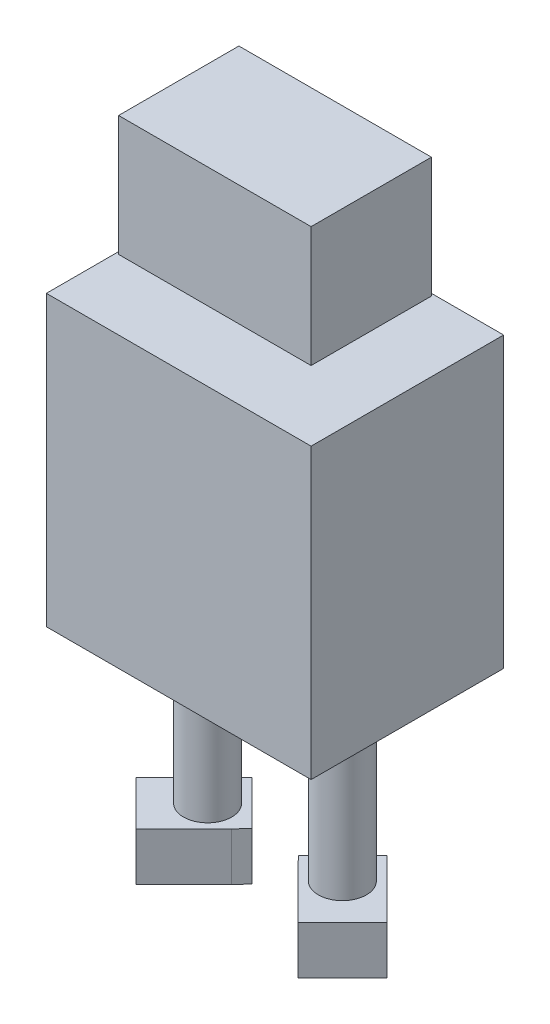
SolidWorks part; units mm, degrees
ref_plane "Front Plane" through (0, 0, 0) normal (0, 0, 1) x (1, 0, 0)
ref_plane "Top Plane" through (0, 0, 0) normal (0, 1, 0) x (1, 0, 0)
ref_plane "Right Plane" through (0, 0, 0) normal (1, 0, 0) x (0, 0, -1)
sketch "Sketch1" plane through (0, 0, 0) normal (0, 0, 1) x (1, 0, 0)
  line L1 (-27.5, -30) -> (27.5, -30)
  line L2 (-27.5, -30) -> (-27.5, 30)
  line L3 (-27.5, 30) -> (27.5, 30)
  line L4 (27.5, -30) -> (27.5, 30)
  line L5 (-27.5, -30) -> (27.5, 30) construction
  line L6 (-27.5, 30) -> (27.5, -30) construction
  point P0 (0, 0)
  dimension "D1" = 60
  dimension "D2" = 55
extrude "Boss-Extrude1" add sketch "Sketch1" along normal blind 40
sketch "Sketch2" plane through (0, 30, 0) normal (0, 1, 0) x (-1, 0, 0)
  line L0 (0, 40) -> (0, 0) construction
  line L1 (-27.5, 40) -> (27.5, 40) construction
  line L2 (-27.5, 0) -> (27.5, 0) construction
  line L3 (-27.5, 20) -> (27.5, 20) construction
  line L4 (-27.5, 40) -> (-27.5, 0) construction
  line L5 (27.5, 40) -> (27.5, 0) construction
  circle A0 centre (0, 20) radius 4
  dimension "D1" = 8
extrude "Boss-Extrude2" add sketch "Sketch2" along normal blind 7
sketch "Sketch4" plane through (0, 37, 0) normal (0, 1, 0) x (1, 0, 0)
  line L1 (20, -7.5) -> (-20, -7.5)
  line L2 (20, -7.5) -> (20, -32.5)
  line L3 (20, -32.5) -> (-20, -32.5)
  line L4 (-20, -7.5) -> (-20, -32.5)
  line L5 (20, -7.5) -> (-20, -32.5) construction
  line L6 (20, -32.5) -> (-20, -7.5) construction
  point P0 (0, -20)
  dimension "D1" = 25
  dimension "D2" = 40
extrude "Boss-Extrude3" add sketch "Sketch4" along normal blind 25
sketch "Sketch5" plane through (0, -30, 0) normal (0, -1, 0) x (1, 0, 0)
  line L0 (27.5, 20) -> (-27.5, 20) construction
  line L1 (27.5, 40) -> (27.5, 0) construction
  line L2 (-27.5, 40) -> (-27.5, 0) construction
  line L3 (0, 20) -> (-14, 20) construction
  line L4 (0, 20) -> (0, 0) construction
  line L5 (-27.5, 0) -> (27.5, 0) construction
  circle A0 centre (-14, 20) radius 5
  circle A1 centre (14, 20) radius 5
  dimension "D2" = 10
  dimension "D1" = 14
extrude "Boss-Extrude4" add sketch "Sketch5" along normal blind 35
sketch "Sketch6" plane through (0, -65, 0) normal (0, -1, 0) x (1, 0, 0)
  line L0 (14, 20) -> (14, 25) construction
  line L1 (14, 25) -> (14, 20) construction
  line L2 (14, 20) -> (19, 20) construction
  line L3 (19, 20) -> (14, 25) construction
  line L4 (14, 25) -> (14, 20) construction
  line L5 (14, 20) -> (16.5, 22.5) construction
  line L6 (14, 20) -> (14, 15) construction
  line L7 (14, 20) -> (9, 20) construction
  line L8 (14, 20) -> (-14.0093, 20) construction
  line L9 (-0.0047, 20) -> (-0.0047, 23.2586) construction
  line L10 (-11.888, 12.8787) -> (-6.888, 17.8787)
  line L11 (-11.888, 12.8787) -> (-14.0093, 10.7574)
  line L12 (9, 20) -> (8.9904, 19.9371)
  line L13 (18.9497, 29.9497) -> (23.9497, 24.9497)
  line L14 (11.8787, 12.8787) -> (6.8787, 17.8787)
  line L15 (6.8787, 22.1213) -> (11.8787, 27.1213)
  line L16 (21.1213, 17.8787) -> (16.1213, 12.8787)
  line L17 (-14.0093, 10.7574) -> (-16.1307, 12.8787)
  line L18 (-21.1307, 17.8787) -> (-16.1307, 12.8787)
  line L19 (23.9497, 24.9497) -> (26.0711, 22.8284)
  line L20 (26.0711, 22.8284) -> (21.1213, 17.8787)
  line L21 (-23.9591, 24.9497) -> (-26.0804, 22.8284)
  line L22 (-26.0804, 22.8284) -> (-21.1307, 17.8787)
  line L23 (16.8284, 32.0711) -> (18.9497, 29.9497)
  line L24 (16.8284, 32.0711) -> (11.8787, 27.1213)
  line L25 (11.8787, 27.1213) -> (12.0293, 27.2794)
  line L26 (6.8787, 17.8787) -> (4.8202, 19.9371)
  line L27 (4.8202, 19.9371) -> (6.8787, 22.1213)
  line L28 (11.8787, 12.8787) -> (14, 10.7574)
  line L29 (14, 10.7574) -> (16.1213, 12.8787)
  line L30 (-16.8378, 32.0711) -> (-18.9591, 29.9497)
  line L31 (-18.9591, 29.9497) -> (-23.9591, 24.9497)
  line L32 (-16.8378, 32.0711) -> (-11.888, 27.1213)
  line L33 (-6.888, 17.8787) -> (-4.8295, 19.9371)
  line L34 (-4.8295, 19.9371) -> (-6.888, 22.1213)
  line L35 (-6.888, 22.1213) -> (-11.888, 27.1213)
  circle A0 centre (14, 20) radius 5 construction
extrude "Boss-Extrude5" add sketch "Sketch6" along normal blind 10 contours L31 L21 L22 L18 L17 L11 L10 L33 L34 L35 L32 L30 | L24 L23 L13 L19 L20 L16 L29 L28 L14 L26 L27 L15
